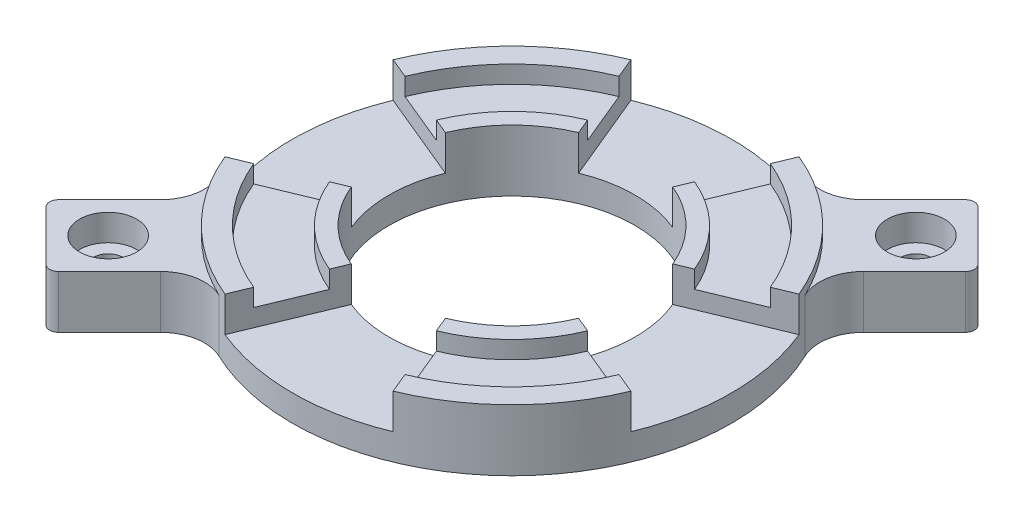
SolidWorks part; units mm, degrees
ref_plane "Front Plane" through (0, 0, 0) normal (0, 0, 1) x (1, 0, 0)
ref_plane "Top Plane" through (0, 0, 0) normal (0, 1, 0) x (1, 0, 0)
ref_plane "Right Plane" through (0, 0, 0) normal (1, 0, 0) x (0, 0, -1)
sketch "Sketch1" plane through (0, 0, 0) normal (0, 1, 0) x (1, 0, 0)
  circle A0 centre (0, 0) radius 25
  circle A1 centre (0, 0) radius 14
  dimension "D1" = 50
  dimension "D2" = 28
extrude "Boss-Extrude1" add sketch "Sketch1" along normal blind 5
sketch "Sketch3" plane through (0, 5, 0) normal (0, 1, 0) x (1, 0, 0)
  circle A0 centre (0, 0) radius 22.5
  circle A1 centre (0, 0) radius 25 construction
  circle A2 centre (0, 0) radius 25
  dimension "D1" = 45
extrude "Boss-Extrude2" add sketch "Sketch3" along normal blind 2
sketch "Sketch5" plane through (0, 5, 0) normal (0, 1, 0) x (1, 0, 0)
  circle A0 centre (0, 0) radius 14 construction
  circle A1 centre (0, 0) radius 14
  circle A2 centre (0, 0) radius 15.9
  dimension "D1" = 31.8
extrude "Boss-Extrude3" add sketch "Sketch5" along normal through all
sketch "Sketch4" plane through (0, 7, 0) normal (0, 1, 0) x (1, 0, 0)
  line L0 (0, 0) -> (-9.5671, 23.097)
  line L1 (0, 0) -> (0, 10.7947) construction
  line L2 (0, 0) -> (9.5671, 23.097)
  circle A0 centre (0, 0) radius 25 construction
  arc A1 (9.5671, 23.097) -> (-9.5671, 23.097) centre (0, 0) ccw
  dimension "D1" = 45
extrude "Cut-Extrude1" cut sketch "Sketch4" against normal blind 4
ref_axis "Axis1" through (0, 7, 0) along (0, -1, 0)
pattern_circular "CirPattern1" count 4 over 360 about axis through (0, 7, 0) along (0, -1, 0) of "Cut-Extrude1"
sketch "Sketch6" plane through (0, 0, 0) normal (0, -1, 0) x (1, 0, 0)
  line L0 (0, 0) -> (-15.9099, 15.9099) construction
  line L1 (-15.9099, 15.9099) -> (-17.6777, 17.6777) construction
  line L2 (-23.097, 9.5671) -> (-20.7873, 8.6104)
  line L3 (-8.6104, 20.7873) -> (-9.5671, 23.097)
  line L4 (-23.097, 9.5671) -> (-20.7873, 8.6104) construction
  line L5 (-8.6104, 20.7873) -> (-9.5671, 23.097) construction
  line L6 (23.097, -9.5671) -> (20.7873, -8.6104)
  line L7 (8.6104, -20.7873) -> (9.5671, -23.097)
  line L8 (23.097, -9.5671) -> (20.7873, -8.6104) construction
  line L9 (8.6104, -20.7873) -> (9.5671, -23.097) construction
  line L10 (-17.6777, 17.6777) -> (-1.6747, 1.6747) construction
  line L11 (-30.052, 22.981) -> (-22.981, 30.052)
  line L12 (-22.981, 30.052) -> (-13.785, 20.856)
  line L13 (-30.052, 22.981) -> (-20.856, 13.785)
  circle A0 centre (0, 0) radius 25 construction
  circle A1 centre (0, 0) radius 25
  circle A2 centre (0, 0) radius 25 construction
  arc A3 (-20.856, 13.785) -> (-13.785, 20.856) centre (0, 0) cw
  arc A4 (-9.5671, 23.097) -> (-23.097, 9.5671) centre (0, 0) ccw
  arc A5 (-8.6104, 20.7873) -> (-20.7873, 8.6104) centre (0, 0) ccw
  arc A6 (-9.5671, 23.097) -> (-23.097, 9.5671) centre (0, 0) ccw construction
  arc A7 (-8.6104, 20.7873) -> (-20.7873, 8.6104) centre (0, 0) ccw construction
  arc A8 (9.5671, -23.097) -> (23.097, -9.5671) centre (0, 0) ccw
  arc A9 (8.6104, -20.7873) -> (20.7873, -8.6104) centre (0, 0) ccw
  arc A10 (9.5671, -23.097) -> (23.097, -9.5671) centre (0, 0) ccw construction
  arc A11 (8.6104, -20.7873) -> (20.7873, -8.6104) centre (0, 0) ccw construction
  dimension "D4" = 10
  dimension "D5" = 12.5
  dimension "D1" = 0
  dimension "D2" = 0
  dimension "D3" = 0
extrude "Boss-Extrude4" add sketch "Sketch6" against normal blind 6
sketch "Sketch7" plane through (0, 6, 0) normal (0, 1, 0) x (1, 0, 0)
  line L0 (-26.5165, -26.5165) -> (-1.2144, -1.2144) construction
  line L1 (-22.981, -30.052) -> (-30.052, -22.981) construction
  line L2 (-13.785, -20.856) -> (-22.981, -30.052) construction
  point P6 (-22.981, -22.981)
  dimension "D1" = 5
hole_wizard "CBORE for M3 SHCS1" positions "Sketch7" profile "Sketch8" counterbore size "M3" standard "ANSI Metric" end condition up to next
sketch "Sketch8" plane through (-22.981, 6, 22.981) normal (1, 0, 0) x (0, 0, 1)
  line L0 (0, 0) -> (0, 6)
  line L1 (0, 6) -> (1.7, 6)
  line L3 (1.7, 6) -> (1.7, 3)
  line L4 (1.7, 3) -> (3.25, 3)
  line L5 (3.25, 3) -> (3.25, 0)
  line L7 (3.25, 0) -> (0, 0)
  line L11 (0, -6.35) -> (0, 107.95) construction
  dimension "Thru Hole Dia." = 3.4
  dimension "Thru Hole Depth" = 6
  dimension "C'Bore Dia." = 6.5
  dimension "C'Bore Depth" = 3
fillet "Fillet1" radius 5 2 edges at (-20.856, 3, 13.785) (-13.785, 3, 20.856)
ref_plane "Plane1" through (0, 0, 0) normal (-0.7071, 0, 0.7071) x (0.7071, 0, 0.7071)
mirror "Mirror1" about plane through (0, 0, 0) normal (-0.7071, 0, 0.7071) of "Fillet1", "CBORE for M3 SHCS1", "Boss-Extrude4"
fillet "Fillet2" radius 1 4 edges at (22.981, 3, -30.052) (30.052, 3, -22.981) (-22.981, 3, 30.052) (-30.052, 3, 22.981)
sketch "Sketch9" plane through (0, 3, 0) normal (0, 1, 0) x (1, 0, 0)
  line L0 (20.7873, 8.6104) -> (14.6897, 6.0847) construction
  line L1 (12.9343, -5.3576) -> (23.097, -9.5671) construction
  arc A0 (17.7385, 7.3475) -> (18.0157, -7.4623) centre (5.9986, -0.2797) cw construction
  arc A1 (12.9343, -5.3576) -> (12.9343, 5.3576) centre (0, 0) ccw construction
  text T0 "<b>1.80</b>" font "Century Gothic" height 3.5
extrude "Cut-Extrude2" [suppressed] cut sketch "Sketch9" against normal blind 0.5
